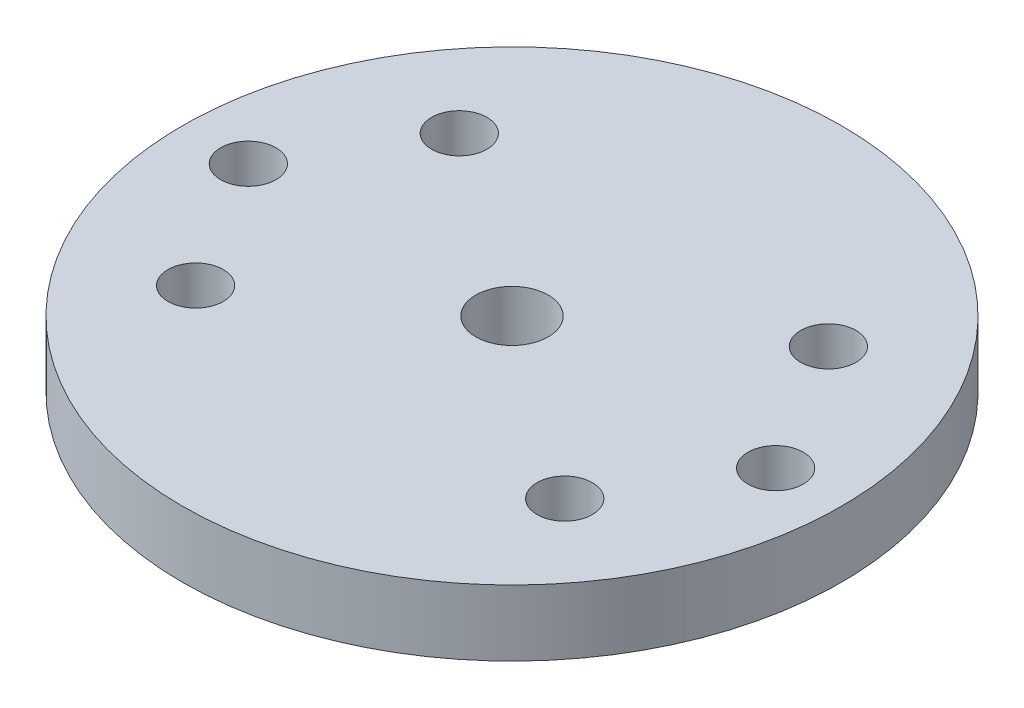
SolidWorks part; units mm, degrees
ref_plane "Front Plane" through (0, 0, 0) normal (0, 0, 1) x (1, 0, 0)
ref_plane "Top Plane" through (0, 0, 0) normal (0, 1, 0) x (1, 0, 0)
ref_plane "Right Plane" through (0, 0, 0) normal (1, 0, 0) x (0, 0, -1)
sketch "Sketch1" plane through (0, 0, 0) normal (0, 1, 0) x (1, 0, 0)
  circle A0 centre (0, 0) radius 31.75
  circle A1 centre (0, 0) radius 3.4925
  dimension "D1" = 63.5
  dimension "D2" = 6.985
extrude "Boss-Extrude1" add sketch "Sketch1" along normal mid plane 6.35
sketch "Sketch2" plane through (0, -3.175, 0) normal (0, -1, 0) x (1, 0, 0)
  circle A0 centre (-17.78, 12.7) radius 2.667 construction
  circle A1 centre (-25.4, 0) radius 2.667 construction
  circle A2 centre (-17.78, -12.7) radius 2.667 construction
  circle A3 centre (17.78, -12.7) radius 2.667 construction
  circle A4 centre (25.4, 0) radius 2.667 construction
  circle A5 centre (17.78, 12.7) radius 2.667 construction
  circle A6 centre (-17.78, 12.7) radius 2.667
  circle A7 centre (-25.4, 0) radius 2.667
  circle A8 centre (-17.78, -12.7) radius 2.667
  circle A9 centre (17.78, -12.7) radius 2.667
  circle A10 centre (25.4, 0) radius 2.667
  circle A11 centre (17.78, 12.7) radius 2.667
  circle A12 centre (-17.78, 12.7) radius 2.2225 construction
  circle A13 centre (-25.4, 0) radius 2.2225 construction
  circle A14 centre (-17.78, -12.7) radius 2.2225 construction
  circle A15 centre (17.78, 12.7) radius 2.2225 construction
  circle A16 centre (25.4, 0) radius 2.2225 construction
  circle A17 centre (17.78, -12.7) radius 2.2225 construction
  dimension "D1" = 4.445
  dimension "D2" = 4.445
  dimension "D3" = 4.445
  dimension "D4" = 4.445
  dimension "D5" = 4.445
  dimension "D6" = 4.445
extrude "Cut-Extrude1" cut sketch "Sketch2" against normal through all
